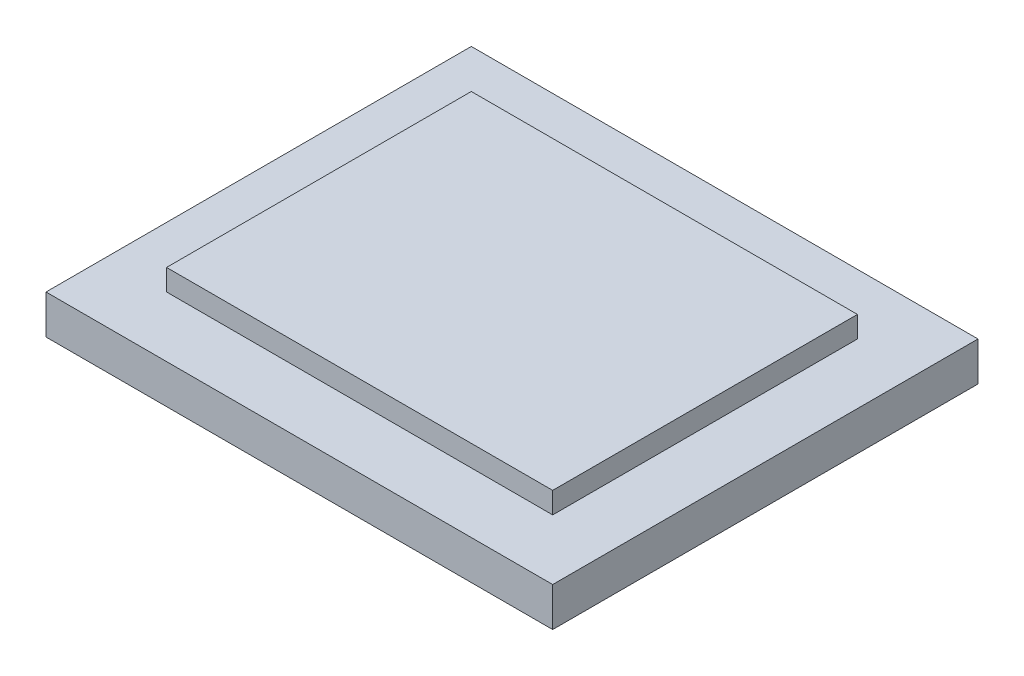
SolidWorks part; units mm, degrees
ref_plane "Front Plane" through (0, 0, 0) normal (0, 0, 1) x (1, 0, 0)
ref_plane "Top Plane" through (0, 0, 0) normal (0, 1, 0) x (1, 0, 0)
ref_plane "Right Plane" through (0, 0, 0) normal (1, 0, 0) x (0, 0, -1)
sketch "Sketch1" plane through (0, 0, 0) normal (0, 1, 0) x (1, 0, 0)
  line L1 (75.65, 63.5) -> (-75.65, 63.5)
  line L2 (75.65, 63.5) -> (75.65, -63.5)
  line L3 (75.65, -63.5) -> (-75.65, -63.5)
  line L4 (-75.65, 63.5) -> (-75.65, -63.5)
  line L5 (75.65, 63.5) -> (-75.65, -63.5) construction
  line L6 (75.65, -63.5) -> (-75.65, 63.5) construction
  point P0 (0, 0)
  dimension "D1" = 127
  dimension "D2" = 151.3
extrude "Boss-Extrude1" add sketch "Sketch1" along normal blind 18
sketch "Sketch2" plane through (0, 18, 0) normal (0, 1, 0) x (1, 0, 0)
  line L0 (-75.65, 63.5) -> (-75.65, -63.5) construction
  line L1 (-75.65, -63.5) -> (75.65, -63.5)
  line L2 (-75.65, -63.5) -> (-75.65, -45.5)
  line L3 (-75.65, -45.5) -> (75.65, -45.5)
  line L4 (75.65, -63.5) -> (75.65, -45.5)
  line L5 (75.65, -63.5) -> (75.65, 63.5) construction
  line L6 (-81.2469, 0) -> (80.8343, 0) construction
  line L7 (75.65, 63.5) -> (75.65, 45.5)
  line L8 (-75.65, 45.5) -> (75.65, 45.5)
  line L9 (-75.65, 63.5) -> (-75.65, 45.5)
  line L10 (-75.65, 63.5) -> (75.65, 63.5)
  point P13 (43.6867, -63.5)
  point P17 (43.6867, 63.5)
  dimension "D1" = 18
sketch "Sketch3" plane through (0, 18, 0) normal (0, 1, 0) x (1, 0, 0)
  line L0 (75.65, 63.5) -> (-75.65, 63.5) construction
  line L1 (75.65, -63.5) -> (57.65, -63.5)
  line L2 (75.65, -63.5) -> (75.65, 63.5)
  line L3 (75.65, 63.5) -> (57.65, 63.5)
  line L4 (57.65, -63.5) -> (57.65, 63.5)
  line L5 (-75.65, -63.5) -> (75.65, -63.5) construction
  line L6 (-75.65, 63.5) -> (-57.65, 63.5)
  line L7 (-75.65, 63.5) -> (-75.65, -63.5)
  line L8 (-75.65, -63.5) -> (-57.65, -63.5)
  line L9 (-57.65, 63.5) -> (-57.65, -63.5)
  dimension "D1" = 18
  dimension "D2" = 18
extrude "Cut-Extrude2" cut sketch "Sketch3" against normal blind 6.35
extrude "Cut-Extrude3" cut sketch "Sketch2" against normal blind 6.35
